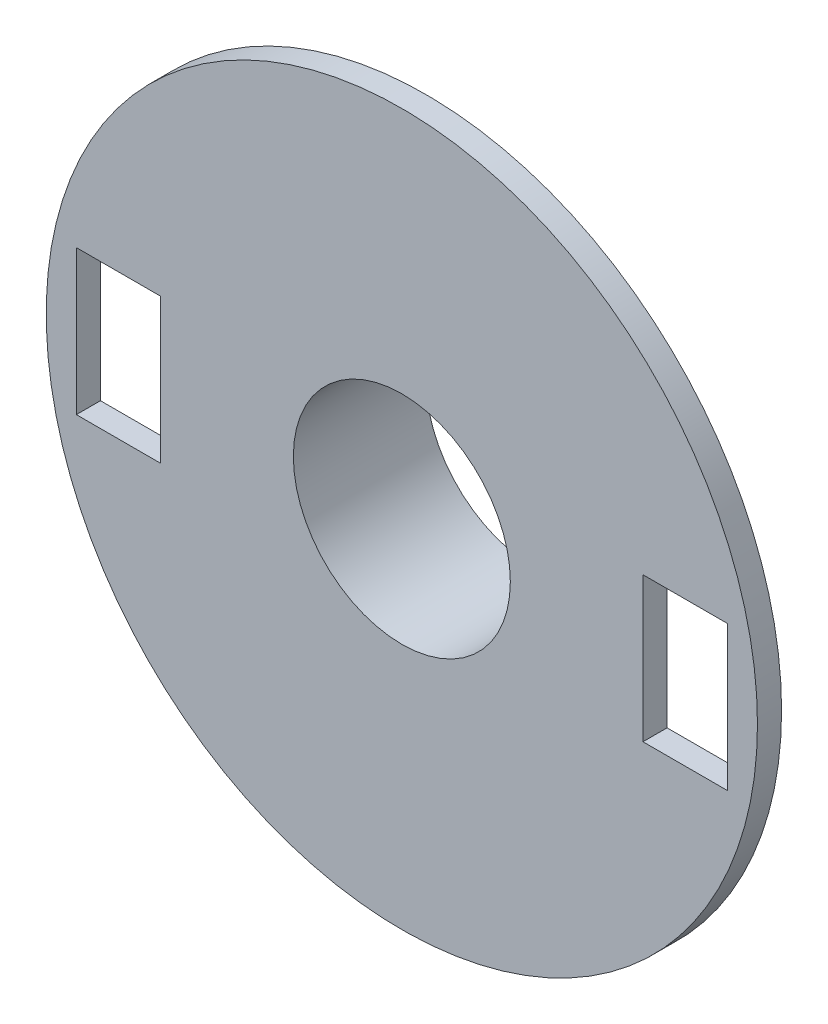
SolidWorks part; units mm, degrees
ref_plane "前视基准面" through (0, 0, 0) normal (0, 0, 1) x (1, 0, 0)
ref_plane "上视基准面" through (0, 0, 0) normal (0, 1, 0) x (1, 0, 0)
ref_plane "右视基准面" through (0, 0, 0) normal (1, 0, 0) x (0, 0, -1)
other "Configuration Table"
sketch "Sketch1" plane through (0, 0, 0) normal (0, 0, 1) x (1, 0, 0)
  circle A0 centre (0, 0) radius 14.75
  dimension "D1" = 29.5
extrude "Boss-Extrude1" add sketch "Sketch1" along normal blind 1
sketch "Sketch2" plane through (0, 0, 0) normal (0, 0, -1) x (-1, 0, 0)
  circle A0 centre (0, 0) radius 5
  dimension "D1" = 10
extrude "Boss-Extrude2" add sketch "Sketch2" along normal blind 4.5
sketch "Sketch3" plane through (0, 0, -4.5) normal (0, 0, -1) x (-1, 0, 0)
  line L0 (0, 0) -> (-17.5641, 0) construction
  line L1 (-13.5, -3) -> (-10, -3)
  line L2 (-13.5, -3) -> (-13.5, 3)
  line L3 (-13.5, 3) -> (-10, 3)
  line L4 (-10, -3) -> (-10, 3)
  line L5 (-13.5, -3) -> (-10, 3) construction
  line L6 (-13.5, 3) -> (-10, -3) construction
  line L7 (0, 0) -> (0, 9.7065) construction
  line L8 (13.5, -3) -> (10, -3)
  line L9 (10, -3) -> (10, 3)
  line L10 (13.5, 3) -> (10, 3)
  line L11 (13.5, -3) -> (13.5, 3)
  circle A0 centre (0, 0) radius 4.5
  point P3 (-11.75, 0)
  dimension "D1" = 9
  dimension "D2" = 10
  dimension "D3" = 3.5
  dimension "D4" = 6
extrude "Cut-Extrude1" cut sketch "Sketch3" against normal through all
